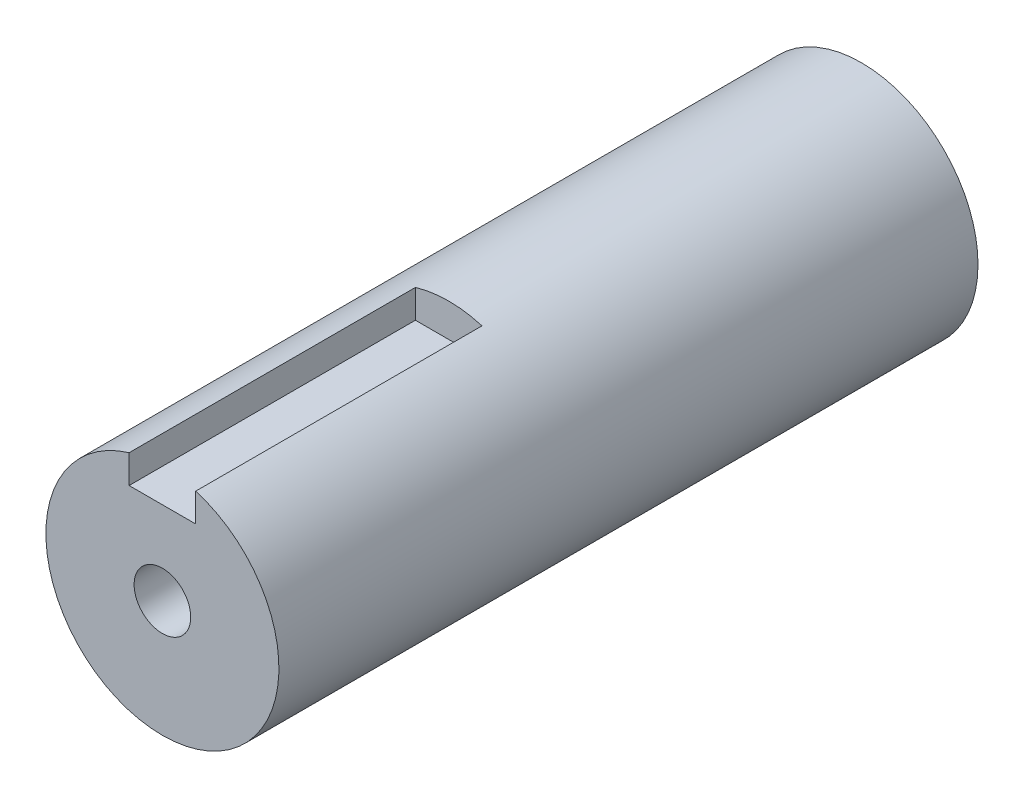
SolidWorks part; units mm, degrees
ref_plane "Plan de face" through (0, 0, 0) normal (0, 0, 1) x (1, 0, 0)
ref_plane "Plan de dessus" through (0, 0, 0) normal (0, 1, 0) x (1, 0, 0)
ref_plane "Plan de droite" through (0, 0, 0) normal (1, 0, 0) x (0, 0, -1)
sketch "Esquisse1" plane through (0, 0, 0) normal (0, 0, 1) x (1, 0, 0)
  circle A0 centre (0, 0) radius 17.5
  dimension "D1" = 35
extrude "Boss.-Extru.1" add sketch "Esquisse1" along normal blind 105
sketch "Esquisse2" plane through (0, 0, 105) normal (0, 0, 1) x (1, 0, 0)
  line L0 (0, 0) -> (0, 17.5) construction
  line L2 (-5, 19.5848) -> (5, 19.5848)
  line L3 (-5, 19.5848) -> (-5, 12.5)
  line L4 (-5, 12.5) -> (5, 12.5)
  line L5 (5, 19.5848) -> (5, 12.5)
  circle A0 centre (0, 0) radius 17.5 construction
  point P10 (0, 12.5)
  dimension "D1" = 10
  dimension "D2" = 5
extrude "Enlèv. mat.-Extru.1" cut sketch "Esquisse2" against normal blind 43
hole_wizard "Trou taraudé M101" positions "Esquisse6" profile "Esquisse5" tap size "M10" standard "ISO"
sketch "Esquisse6" plane through (0, 0, 105) normal (0, 0, 1) x (1, 0, 0)
  point P0 (0, 0)
sketch "Esquisse5" plane through (0, 0, 105) normal (1, 0, 0) x (0, -1, 0)
  line L0 (0, 0) -> (0, 42.5537)
  line L1 (0, 42.5537) -> (4.25, 40)
  line L2 (4.25, 40) -> (4.25, 0)
  line L5 (4.25, 0) -> (0, 0)
  line L10 (0, 42.5537) -> (-4.25, 40) construction
  line L11 (0, -6.35) -> (0, 107.95) construction
  dimension "Diamètre du trou pour taraudage" = 8.5
  dimension "Profondeur du trou pour taraudage" = 40
  dimension "Angle de pointe" = 118
cosmetic thread "Filetage de perçage3" parameters "D1"=38.5, "D2"=10
